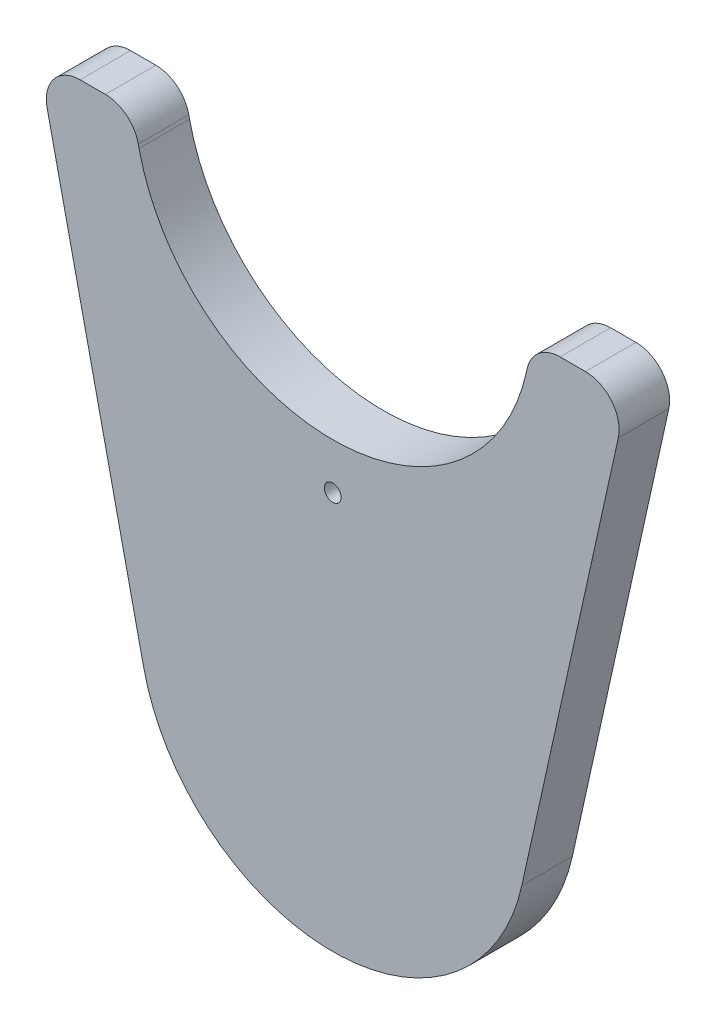
SolidWorks part; units mm, degrees
ref_plane "Front" through (0, 0, 0) normal (0, 0, 1) x (1, 0, 0)
ref_plane "Top" through (0, 0, 0) normal (0, 1, 0) x (1, 0, 0)
ref_plane "Right" through (0, 0, 0) normal (1, 0, 0) x (0, 0, -1)
sketch "Sketch1" plane through (0, 0, 0) normal (0, 0, 1) x (1, 0, 0)
  line L0 (56.1416, -12.4244) -> (84.78, 116.9824)
  line L2 (-56.1416, -12.4244) -> (-84.78, 116.9824)
  line L3 (-75.0162, 129.1431) -> (-67.4954, 129.1431)
  line L4 (57.5028, 120.2743) -> (57.7306, 121.3039)
  line L5 (-57.4972, 120.2447) -> (-57.7316, 121.3039)
  line L7 (67.4944, 129.1431) -> (75.0162, 129.1431)
  arc A0 (-56.1416, -12.4244) -> (56.1416, -12.4244) centre (0, 0) ccw
  arc A1 (-57.4972, 120.2447) -> (57.5028, 120.2743) centre (-0.0005, 133) ccw
  arc A2 (84.78, 116.9824) -> (75.0162, 129.1431) centre (75.0162, 119.1431) ccw
  arc A3 (57.7306, 121.3039) -> (67.4944, 129.1431) centre (67.4944, 119.1431) cw
  arc A4 (-57.7316, 121.3039) -> (-67.4954, 129.1431) centre (-67.4954, 119.1431) ccw
  arc A5 (-75.0162, 129.1431) -> (-84.78, 116.9824) centre (-75.0162, 119.1431) ccw
  circle A7 centre (0, 60.5) radius 2.5
  point P15 (87.4712, 129.1431)
  point P19 (59.4655, 129.1431)
  point P24 (-87.4712, 129.1431)
  dimension "D1" = 115
  dimension "D2" = 115
  dimension "D3" = 141.5675
  dimension "D5" = 133
  dimension "D8" = 10
  dimension "D9" = 5
  dimension "D10" = 60.5
  dimension "D6" = 27.3441
  dimension "D7" = 27.3431
extrude "Boss-Extrude1" add sketch "Sketch1" along normal blind 15
